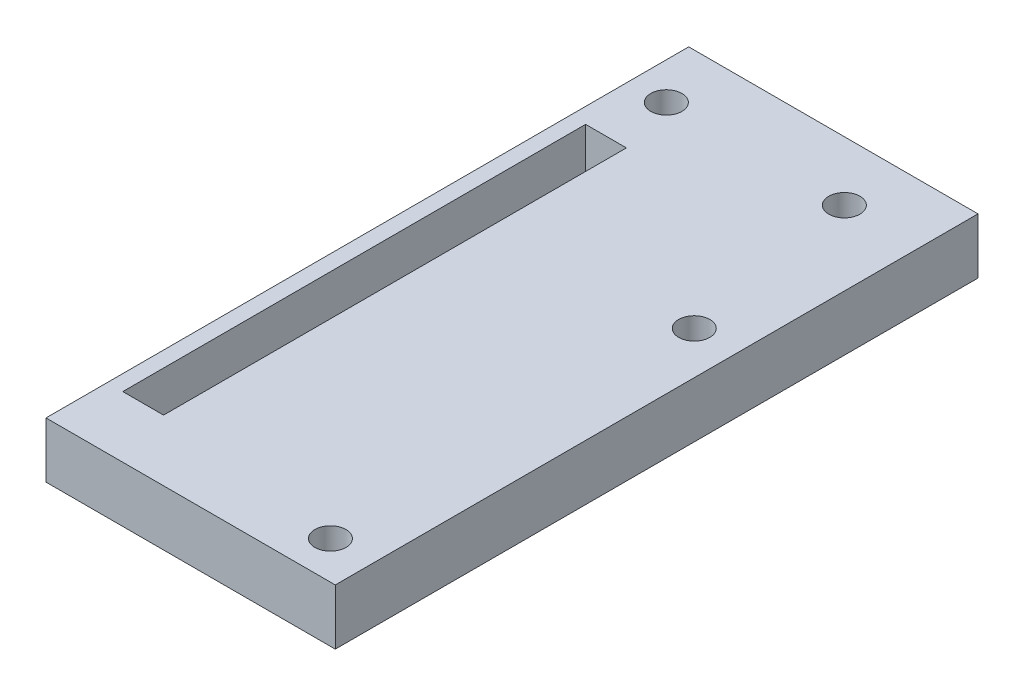
SolidWorks part; units mm, degrees
ref_plane "Front Plane" through (0, 0, 0) normal (0, 0, 1) x (1, 0, 0)
ref_plane "Top Plane" through (0, 0, 0) normal (0, 1, 0) x (1, 0, 0)
ref_plane "Right Plane" through (0, 0, 0) normal (1, 0, 0) x (0, 0, -1)
sketch "Sketch1" plane through (0, 0, 0) normal (0, 1, 0) x (1, 0, 0)
  line L1 (25, 43.325) -> (-25, 43.325)
  line L2 (25, 43.325) -> (25, -43.325)
  line L3 (25, -43.325) -> (-25, -43.325)
  line L4 (-25, 43.325) -> (-25, -43.325)
  line L5 (25, 43.325) -> (-25, -43.325) construction
  line L6 (25, -43.325) -> (-25, 43.325) construction
  point P0 (0, 0)
  dimension "D1" = 86.65
  dimension "D2" = 50
extrude "Boss-Extrude1" add sketch "Sketch1" along normal blind 7.5
sketch "Sketch7" plane through (0, 7.5, 0) normal (0, 1, 0) x (1, 0, 0)
  line L0 (-5.4, 27.325) -> (-5.4, -35.075)
  line L1 (-5.4, -35.075) -> (-10.9, -35.075)
  line L2 (-10.9, -35.075) -> (-10.9, 27.325)
  line L3 (-10.9, 27.325) -> (-5.4, 27.325)
  line L6 (25, 43.325) -> (-25, 43.325) construction
  line L7 (25, -43.325) -> (25, 43.325) construction
  dimension "D1" = 30.4
  dimension "D2" = 16
  dimension "D3" = 5.5
  dimension "D4" = 62.4
extrude "Cut-Extrude5" cut sketch "Sketch7" against normal blind 5.95 contours L0 L1 L2 L3
sketch "Sketch11" plane through (0, 7.5, 0) normal (0, 1, 0) x (1, 0, 0)
  line L0 (25, -43.325) -> (25, 43.325) construction
  line L1 (25, 43.325) -> (-25, 43.325) construction
  circle A0 centre (15.982, 35.325) radius 2.1
  circle A1 centre (-8.018, 35.325) radius 2.1
  dimension "D3" = 4.2
  dimension "D4" = 4.2
  dimension "D1" = 9.018
  dimension "D2" = 33.018
  dimension "D5" = 8
  dimension "D6" = 8
extrude "Cut-Extrude8" cut sketch "Sketch11" against normal through all
sketch "Sketch12" plane through (0, 7.5, 0) normal (0, 1, 0) x (1, 0, 0)
  line L0 (-5.4, 27.325) -> (-5.4, -35.075) construction
  line L1 (-5.4, 27.325) -> (-5.4, -35.075) construction
  line L2 (25, 43.325) -> (-25, 43.325) construction
  circle A0 centre (20.25, 10.821) radius 2.1
  circle A1 centre (20.25, -38.229) radius 2.1
  dimension "D3" = 49.05
  dimension "D5" = 4.2
  dimension "D6" = 4.2
  dimension "D1" = 25.65
  dimension "D2" = 25.65
  dimension "D4" = 32.504
extrude "Cut-Extrude10" cut sketch "Sketch12" against normal through all
sketch "Sketch13" plane through (25, 0, 0) normal (1, 0, 0) x (0, 0, -1)
  line L1 (-43.325, 7.5) -> (43.325, 7.5)
  line L2 (-43.325, 7.5) -> (-43.325, 0)
  line L3 (-43.325, 0) -> (43.325, 0)
  line L4 (43.325, 7.5) -> (43.325, 0)
extrude "Boss-Extrude2" add sketch "Sketch13" along normal blind 1
sketch "Sketch14" plane through (-25, 0, 0) normal (-1, 0, 0) x (0, 0, 1)
  line L1 (-43.325, 7.5) -> (43.325, 7.5)
  line L2 (-43.325, 7.5) -> (-43.325, 0)
  line L3 (-43.325, 0) -> (43.325, 0)
  line L4 (43.325, 7.5) -> (43.325, 0)
extrude "Cut-Extrude11" cut sketch "Sketch14" against normal blind 12
